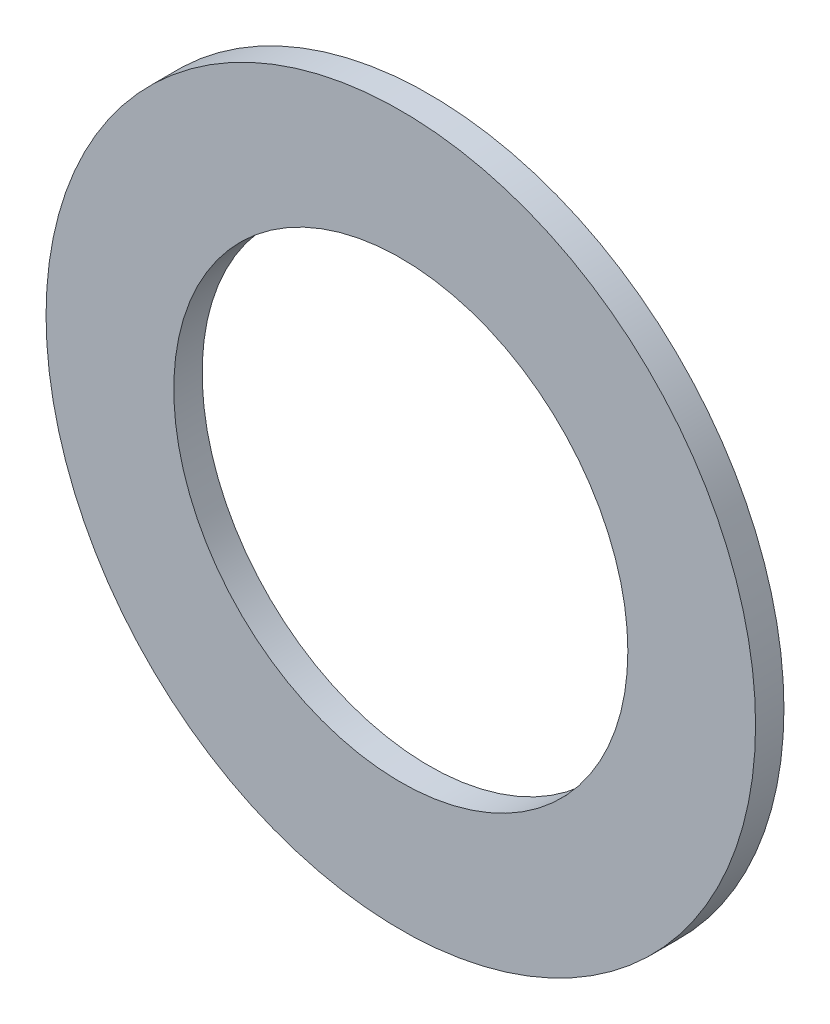
SolidWorks part; units mm, degrees
ref_plane "Front Plane" through (0, 0, 0) normal (0, 0, 1) x (1, 0, 0)
ref_plane "Top Plane" through (0, 0, 0) normal (0, 1, 0) x (1, 0, 0)
ref_plane "Right Plane" through (0, 0, 0) normal (1, 0, 0) x (0, 0, -1)
sketch "Sketch1" plane through (0, 0, 0) normal (0, 0, 1) x (1, 0, 0)
  circle A0 centre (0, 0) radius 2.032
  circle A1 centre (0, 0) radius 3.175
  point P4 (-2.032, 0)
  dimension "ID" = 4.064
  dimension "OD" = 6.35
extrude "Extrude1" add sketch "Sketch1" against normal blind 0.254
